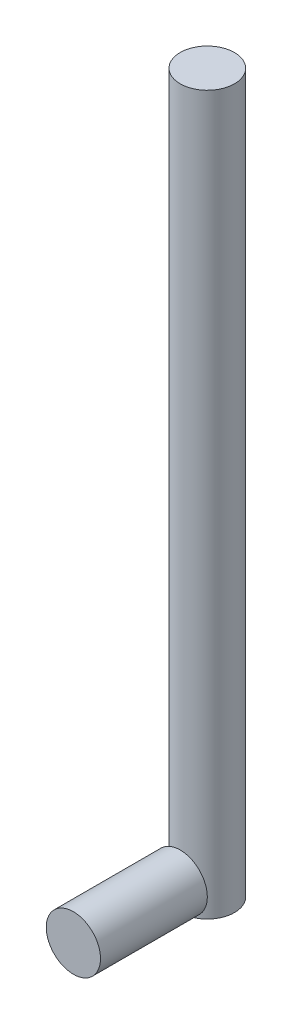
SolidWorks part; units mm, degrees
ref_plane "Front Plane" through (0, 0, 0) normal (0, 0, 1) x (1, 0, 0)
ref_plane "Top Plane" through (0, 0, 0) normal (0, 1, 0) x (1, 0, 0)
ref_plane "Right Plane" through (0, 0, 0) normal (1, 0, 0) x (0, 0, -1)
sketch "Sketch1" plane through (0, 0, 0) normal (0, 1, 0) x (1, 0, 0)
  circle A0 centre (0, 0) radius 6.5
  dimension "D1" = 13
extrude "Boss-Extrude1" add sketch "Sketch1" along normal blind 172
ref_plane "Plane1" through (0, 0, 6.5) normal (0, 0, 1) x (1, 0, 0)
sketch "Sketch2" plane through (0, 0, 6.5) normal (0, 0, 1) x (1, 0, 0)
  line L0 (-6.5, 0) -> (6.5, 0) construction
  circle A0 centre (0, 6.5) radius 6.5
  dimension "D1" = 13
extrude "Boss-Extrude2" add sketch "Sketch2" along normal blind 25.6 separate body
